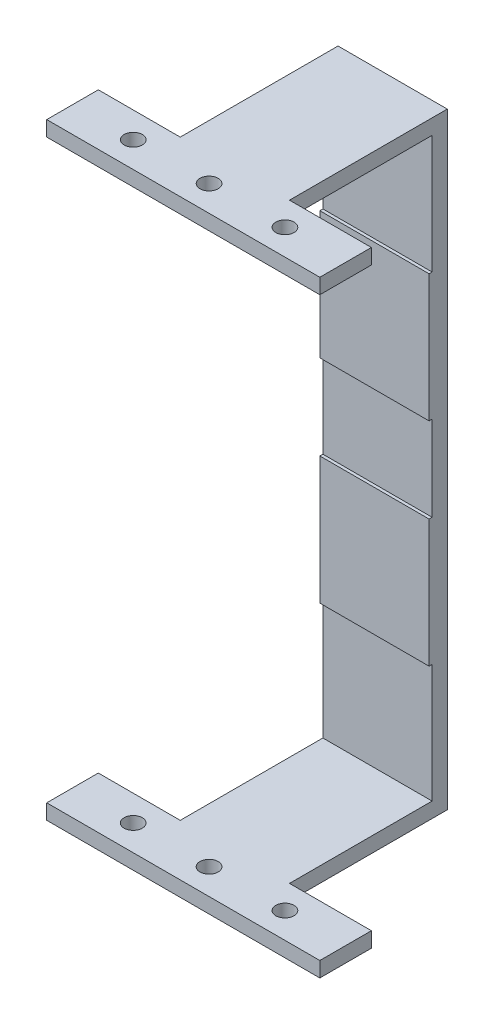
SolidWorks part; units mm, degrees
ref_plane "Alzado" through (0, 0, 0) normal (0, 0, 1) x (1, 0, 0)
ref_plane "Planta" through (0, 0, 0) normal (0, 1, 0) x (1, 0, 0)
ref_plane "Vista lateral" through (0, 0, 0) normal (1, 0, 0) x (0, 0, -1)
sketch "Croquis1" plane through (0, 0, 0) normal (0, 0, 1) x (1, 0, 0)
  line L1 (-45, 100) -> (45, 100)
  line L2 (-45, 100) -> (-45, -100)
  line L3 (-45, -100) -> (45, -100)
  line L4 (45, 100) -> (45, -100)
  line L5 (-45, 100) -> (45, -100) construction
  line L6 (-45, -100) -> (45, 100) construction
  point P0 (0, 0)
  dimension "D1" = 90
  dimension "D2" = 200
extrude "Saliente-Extruir1" add sketch "Croquis1" against normal blind 5
sketch "Croquis2" plane through (0, 0, 0) normal (0, 0, 1) x (1, 0, 0)
  line L0 (45, -100) -> (45, 100) construction
  line L1 (-45, 100) -> (45, 100)
  line L2 (-45, 100) -> (-45, 95)
  line L3 (-45, 95) -> (45, 95)
  line L4 (45, 100) -> (45, 95)
  line L6 (-45, -100) -> (45, -100)
  line L7 (-45, -100) -> (-45, -95)
  line L8 (-45, -95) -> (45, -95)
  line L9 (45, -100) -> (45, -95)
  dimension "D1" = 5
  dimension "D2" = 5
extrude "Saliente-Extruir2" add sketch "Croquis2" along normal blind 64
sketch "Croquis3" plane through (0, 0, 0) normal (0, 0, 1) x (1, 0, 0)
  line L0 (-45, 0) -> (45, 0) construction
  line L1 (-45, 95) -> (-45, -95) construction
  line L2 (45, -95) -> (45, 95) construction
  line L3 (0, 95) -> (0, -95) construction
  line L4 (-45, 95) -> (45, 95) construction
  line L5 (45, -95) -> (-45, -95) construction
  line L6 (-45, -35) -> (45, -35) construction
  line L7 (-45, 35) -> (45, 35) construction
  line L8 (-18, -14) -> (18, -56) construction
  line L9 (27, 95) -> (27, -95) construction
  line L11 (-18, 14) -> (18, 14)
  line L12 (-18, 14) -> (-18, 56)
  line L13 (-18, 56) -> (18, 56)
  line L14 (18, 14) -> (18, 56)
  line L15 (-18, 14) -> (18, 56) construction
  line L16 (-18, 56) -> (18, 14) construction
  line L24 (18, -14) -> (18, -56)
  line L25 (-18, -14) -> (18, -14)
  line L26 (-18, -14) -> (-18, -56)
  line L27 (18, -56) -> (-18, -56)
  line L28 (18, -14) -> (-18, -56) construction
  point P16 (0, -35)
  point P20 (0, 35)
  dimension "D4" = 18
  dimension "D5" = 36
  dimension "D6" = 42
  dimension "D1" = 35
  dimension "D2" = 35
extrude "Saliente-Extruir3" add sketch "Croquis3" along normal blind 1
sketch "Croquis4" plane through (0, 100, 0) normal (0, 1, 0) x (1, 0, 0)
  line L0 (45, -64) -> (-45, -64) construction
  circle A0 centre (-25, -55.5) radius 3
  circle A1 centre (0, -55.5) radius 3
  circle A2 centre (25, -55.5) radius 3
  point P9 (0, -64)
  dimension "D1" = 6
  dimension "D2" = 6
  dimension "D3" = 6
  dimension "D4" = 8.5
  dimension "D5" = 8.5
  dimension "D6" = 8.5
  dimension "D7" = 25
  dimension "D8" = 25
extrude "Cortar-Extruir1" cut sketch "Croquis4" against normal through all
sketch "Croquis5" plane through (0, 0, 0) normal (0, 0, 1) x (1, 0, 0)
  line L0 (45, -95) -> (-45, -95) construction
  line L1 (-45, 95) -> (-18, 95)
  line L2 (-45, 95) -> (-45, -95)
  line L3 (-45, -95) -> (-18, -95)
  line L4 (-18, 95) -> (-18, -95)
  line L5 (-45, 95) -> (45, 95) construction
  line L6 (45, 95) -> (18, 95)
  line L7 (45, 95) -> (45, -95)
  line L8 (45, -95) -> (18, -95)
  line L9 (18, 95) -> (18, -95)
  line L10 (-18, 56) -> (-18, 14) construction
  line L11 (18, 14) -> (18, 56) construction
extrude "Cortar-Extruir3" cut sketch "Croquis5" against normal through all
sketch "Croquis6" plane through (0, 100, 0) normal (0, 1, 0) x (1, 0, 0)
  line L0 (45, 5) -> (18, 5) construction
  line L1 (45, 5) -> (18, 5)
  line L2 (45, 5) -> (45, -47)
  line L3 (45, -47) -> (18, -47)
  line L4 (18, 5) -> (18, -47)
  line L5 (45, 5) -> (18, 5)
  line L6 (45, -64) -> (-45, -64) construction
  line L7 (0, -64) -> (0, 5) construction
  line L8 (45, 5) -> (-45, 5) construction
  line L9 (-45, -47) -> (-18, -47)
  line L10 (-18, 5) -> (-18, -47)
  line L11 (-45, 5) -> (-18, 5)
  line L12 (-45, 5) -> (-45, -47)
  line M13 (-45, 5) -> (-45, -64)
  line M16 (45, 5) -> (-45, 5)
  dimension "D1" = 17
extrude "Cortar-Extruir4" cut sketch "Croquis6" against normal through all contours L10 L9 M16 M13 | L2 L1 L4 L3
